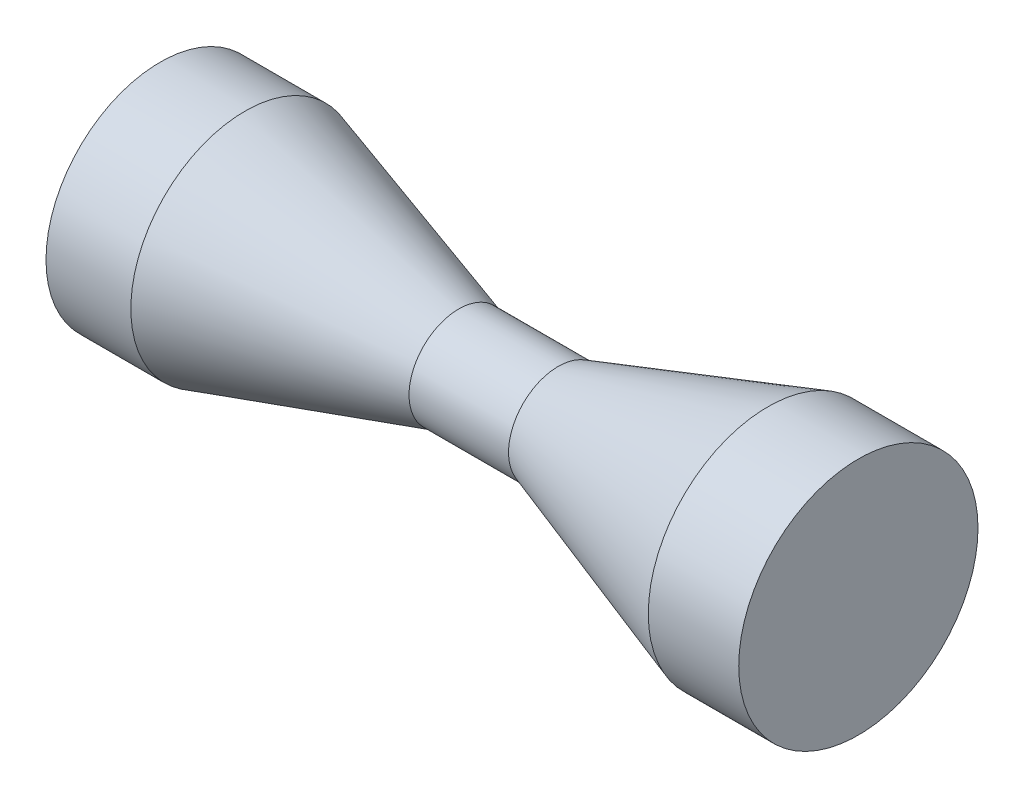
SolidWorks part; units mm, degrees
ref_plane "Front Plane"
ref_plane "Top Plane" through (0, 0, 0) normal (0, 1, 0) x (1, 0, 0)
ref_plane "Right Plane" through (0, 0, 0) normal (1, 0, 0) x (0, 0, -1)
sketch "Sketch1" plane through (0, 0, 0) normal (0, 0, 1) x (1, 0, 0)
  line L0 (-49.6894, 17.6042) -> (-38.6158, 17.6042)
  line L1 (-38.6158, 17.6042) -> (-5.6788, 7.6664)
  line L2 (-5.6788, 7.6664) -> (9.6539, 7.6664)
  line L3 (9.6539, 7.6664) -> (41.9687, 18.438)
  line L4 (41.9687, 18.438) -> (53.905, 18.438)
  line L5 (0, 0) -> (-55.2675, 0) construction
revolve "Revolve-Thin2" add sketch "Sketch1" angle 360 about L5
sketch "Sketch2" plane through (-49.6894, 0, 0) normal (-1, 0, 0) x (0, 0, 1)
  circle A1 centre (0, 0) radius 17.6042
  circle A2 centre (0, 0) radius 17.6042
  dimension "D1" = 0
extrude "Boss-Extrude1" add sketch "Sketch2" along normal blind 2 contours A2
sketch "Sketch3" plane through (53.905, 0, 0) normal (1, 0, 0) x (0, 0, -1)
  circle A1 centre (0, 0) radius 18.438
  circle A2 centre (0, 0) radius 18.438
  dimension "D1" = 0
extrude "Boss-Extrude2" add sketch "Sketch3" along normal blind 2
sketch "Sketch4" plane through (0, 0, 0) normal (0, 0, 1) x (1, 0, 0)
  point P0 (2.1078, 3.3532)
  point P1 (-33.9023, 11.6632)
  point P2 (2.1078, 0)
  point P3 (-33.9023, 0)
  point P4 (2.1078, -3.2074)
  point P5 (-33.9023, -11.3716)
  point P6 (38.1179, 11.6632)
  point P7 (38.1179, 0)
  point P8 (38.1179, -11.3716)
